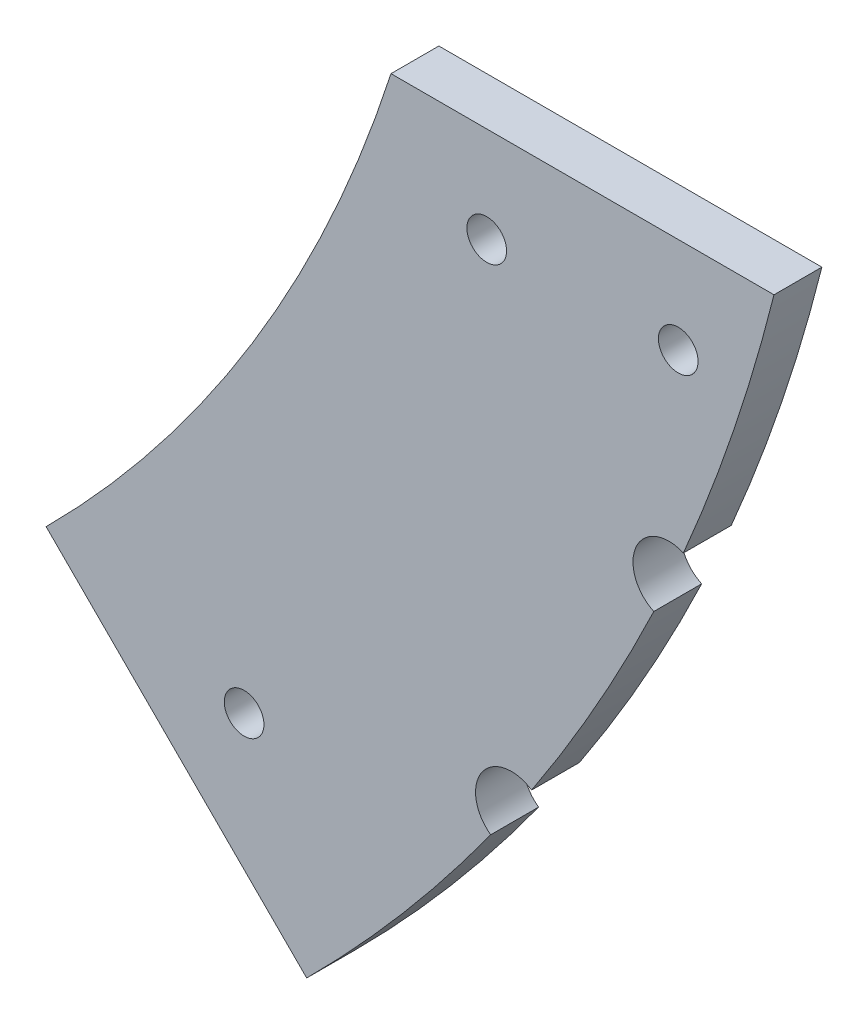
SolidWorks part; units mm, degrees
material "PC High Viscosity"
ref_plane "Front Plane" through (0, 0, 0) normal (0, 0, 1) x (1, 0, 0)
ref_plane "Top Plane" through (0, 0, 0) normal (0, 1, 0) x (1, 0, 0)
ref_plane "Right Plane" through (0, 0, 0) normal (1, 0, 0) x (0, 0, -1)
sketch "Sketch1" plane through (0, 0, 0) normal (0, 0, 1) x (1, 0, 0)
  line L0 (0, 0) -> (177.8, 0) construction
  line L1 (177.8, 0) -> (177.8, -57.15) construction
  line L2 (0, 0) -> (125.7236, -125.7236) construction
  line L3 (125.7236, -125.7236) -> (132.0586, -132.0586) construction
  line L4 (0, 0) -> (177.8, -57.15) construction
  line L5 (125.7236, -125.7236) -> (153.5488, -92.7939) construction
  line L6 (153.5488, -92.7939) -> (177.8, -57.15) construction
  line L7 (0, 0) -> (60.8112, 167.0773) construction
  line L8 (177.8, -57.15) -> (228.6, -57.15)
  line L9 (132.0586, -132.0586) -> (166.6195, -166.6195)
  line L10 (190.5, -69.85) -> (215.9, -69.85) construction
  line L11 (149.339, -149.339) -> (158.3193, -140.3588) construction
  arc A0 (177.8, -57.15) -> (132.0586, -132.0586) centre (0, 0) cw
  arc A1 (177.8, 0) -> (60.8112, 167.0773) centre (0, 0) ccw construction
  arc A2 (228.6, -57.15) -> (166.6195, -166.6195) centre (0, 0) cw
  circle A3 centre (190.5, -69.85) radius 2.6289
  circle A4 centre (215.9, -69.85) radius 2.6289
  circle A5 centre (158.3193, -140.3588) radius 2.6289
  dimension "D6" = 50.8
  dimension "D5" = 70
  dimension "D7" = 12.7
  dimension "D8" = 12.7
  dimension "D9" = 25.4
  dimension "D10" = 5.2578
  dimension "D11" = 5.2578
  dimension "D13" = 5.2578
  dimension "D1" = 177.8
  dimension "D2" = 57.15
  dimension "D3" = 45
  dimension "D4" = 177.8
  dimension "D12" = 12.7
extrude "Boss-Extrude1" add sketch "Sketch1" along normal blind 6.35
sketch "Sketch2" plane through (0, 0, 6.35) normal (0, 0, 1) x (1, 0, 0)
  line L0 (0, 0) -> (214.6615, -97.1828) construction
  line L1 (0, 0) -> (193.7761, -134.0706) construction
  line L2 (166.6195, -166.6195) -> (193.7761, -134.0706) construction
  line L3 (193.7761, -134.0706) -> (214.6615, -97.1828) construction
  line L4 (214.6615, -97.1828) -> (228.6, -57.15) construction
  arc A0 (166.6195, -166.6195) -> (228.6, -57.15) centre (0, 0) ccw construction
  circle A1 centre (193.7761, -134.0706) radius 4.7625
  circle A2 centre (214.6615, -97.1828) radius 4.7625
  dimension "D1" = 9.525
  dimension "D2" = 9.525
extrude "Cut-Extrude1" cut sketch "Sketch2" against normal blind 6.35
